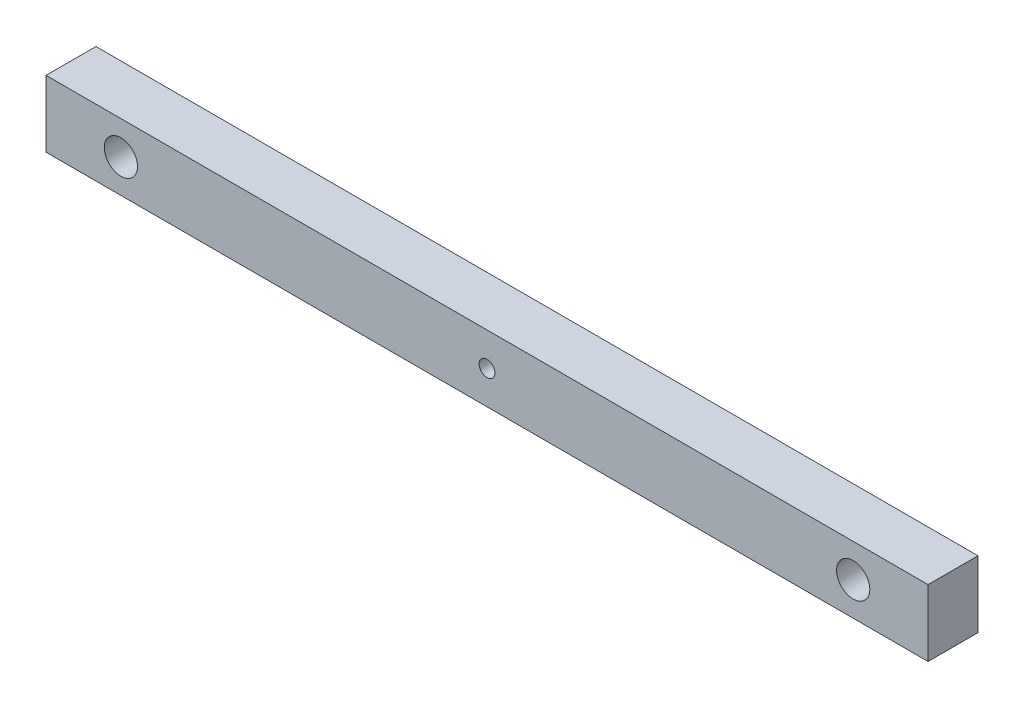
SolidWorks part; units mm, degrees
ref_plane "Front Plane" through (0, 0, 0) normal (0, 0, 1) x (1, 0, 0)
ref_plane "Top Plane" through (0, 0, 0) normal (0, 1, 0) x (1, 0, 0)
ref_plane "Right Plane" through (0, 0, 0) normal (1, 0, 0) x (0, 0, -1)
sketch "Sketch1" plane through (0, 0, 0) normal (0, 0, 1) x (1, 0, 0)
  line L1 (-38.9122, -2) -> (14.0878, -2)
  line L2 (-38.9122, -2) -> (-38.9122, 2)
  line L3 (-38.9122, 2) -> (14.0878, 2)
  line L4 (14.0878, -2) -> (14.0878, 2)
  point P0 (0, 0)
  dimension "D1" = 4
  dimension "D2" = 53
extrude "Boss-Extrude2" add sketch "Sketch1" along normal blind 3 contours L1 L4 L3 L2
sketch "Sketch3" plane through (0, 0, 3) normal (0, 0, 1) x (1, 0, 0)
  line L0 (-38.9122, -2) -> (-38.9122, 2) construction
  line L2 (14.0878, -2) -> (14.0878, 2) construction
  circle A0 centre (-34.4122, 0) radius 1
  circle A1 centre (9.5878, 0) radius 1
  dimension "D2" = 2
  dimension "D4" = 2
  dimension "D1" = 4.5
  dimension "D3" = 4.5
extrude "Cut-Extrude2" cut sketch "Sketch3" against normal blind 3
sketch "Sketch4" plane through (0, 0, 0) normal (0, 0, -1) x (-1, 0, 0)
  line L1 (38.9122, -2) -> (38.9122, 2) construction
  circle A0 centre (12.4122, 0) radius 0.475
  dimension "D2" = 0.95
  dimension "D1" = 26.5
extrude "Cut-Extrude3" cut sketch "Sketch4" against normal blind 3
